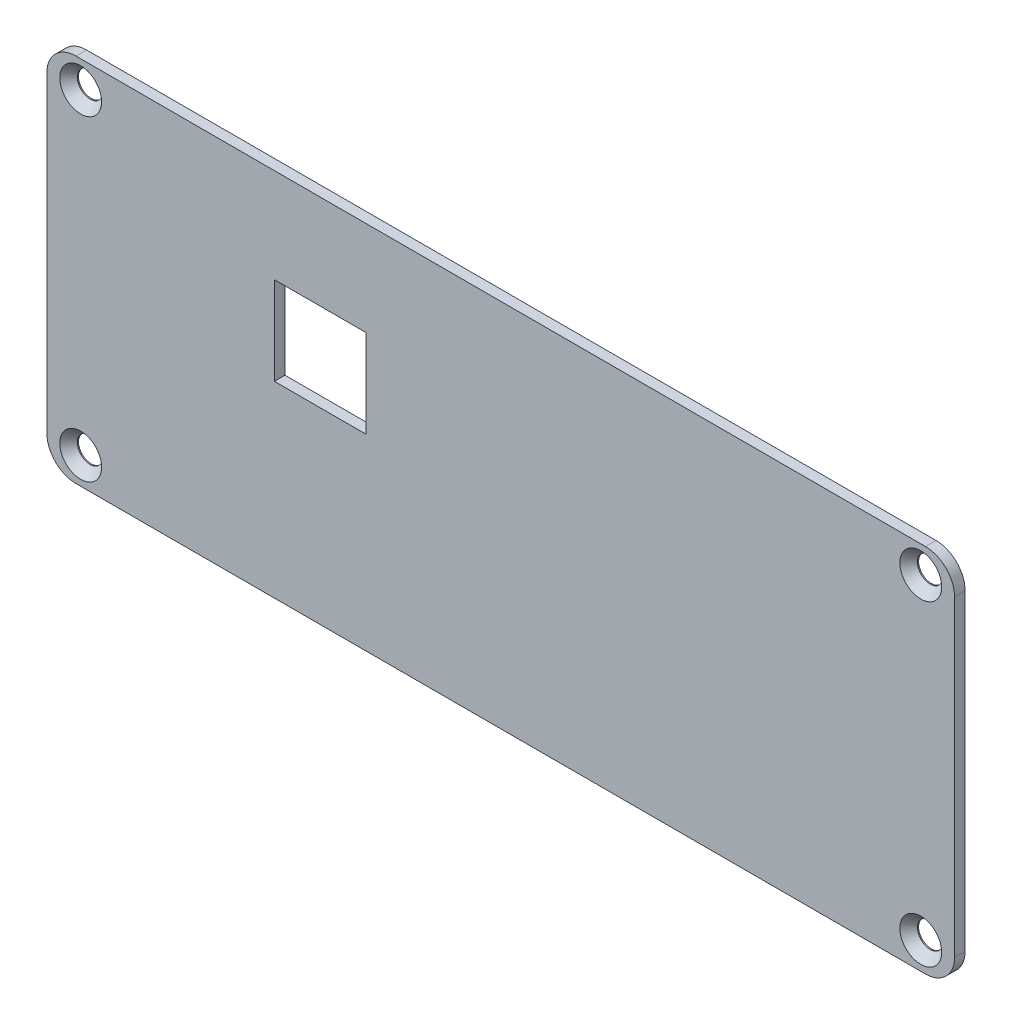
SolidWorks part; units mm, degrees
other "Markup1"
sketch "Sketch3" plane through (0, 0, 0) normal (-0.9973, 0.0561, -0.0476) x (-0.0483, -0.0106, 0.9988)
ref_plane "Front Plane" through (0, 0, 0) normal (0, 0, 1) x (1, 0, 0)
ref_plane "Top Plane" through (0, 0, 0) normal (0, 1, 0) x (1, 0, 0)
ref_plane "Right Plane" through (0, 0, 0) normal (1, 0, 0) x (0, 0, -1)
sketch "Sketch1" plane through (0, 0, 0) normal (0, 0, 1) x (1, 0, 0)
  line L1 (0, 0) -> (124.8, 0)
  line L2 (0, 0) -> (0, -50.9)
  line L3 (0, -50.9) -> (124.8, -50.9)
  line L4 (124.8, 0) -> (124.8, -50.9)
  line L17 (31.285, -12.985) -> (43.885, -12.985)
  line L18 (31.285, -12.985) -> (31.285, -25.085)
  line L19 (31.285, -25.085) -> (43.885, -25.085)
  line L20 (43.885, -12.985) -> (43.885, -25.085)
  point P5 (37.585, -19.035)
  point P6 (0, 0)
  point P7 (37.585, -12.985)
  point P8 (43.885, -19.035)
  dimension "D1" = 124.8
  dimension "D2" = 50.9
  dimension "D3" = 37.585
  dimension "D4" = 19.035
  dimension "D5" = 37.585
  dimension "D6" = 19.035
  dimension "D7" = 12.6
  dimension "D8" = 12.1
extrude "Boss-Extrude1" add sketch "Sketch1" along normal blind 1.45
hole_wizard "CSK for M3.5 Flat Head Machine Screw1" positions "3DSketch1" profile "Sketch2" countersink size "M3.5" standard "ANSI Metric" end condition through all
sketch3d "3DSketch1"
  line L3 (0, 0, 1.45) -> (124.8, 0, 1.45) construction
  line L4 (124.8, 0, 1.45) -> (124.8, -50.9, 1.45) construction
  point P0 (4.65, -3.7, 1.45)
  point P2 (120.15, -3.7, 1.45)
  point P4 (120.15, -47.2, 1.45)
  point P6 (4.65, -47.2, 1.45)
  point P18 (0, 0, 0)
  point P19 (0, 0, 0)
  point P20 (0, 0, 0)
  point P21 (0, 0, 0)
  point P22 (0, 0, 0)
  point P23 (0, 0, 0)
  point P24 (0, 0, 0)
  point P25 (0, 0, 0)
  point P26 (0, 0, 0)
  dimension "D1" = 115.5
  dimension "D2" = 43.5
  dimension "D3" = 3.7
  dimension "D4" = 4.65
sketch "Sketch2" plane through (4.65, -3.7, 1.45) normal (1, 0, 0) x (0, -1, 0)
  line L0 (0, 0) -> (0, 1.45)
  line L1 (0, 1.45) -> (1.75, 1.45)
  line L2 (1.75, 1.45) -> (1.75, 1.2942)
  line L3 (1.75, 1.2942) -> (2.875, 0)
  line L5 (2.875, 0) -> (0, 0)
  line L6 (-1.75, 1.2942) -> (-2.875, 0) construction
  line L11 (0, -6.35) -> (0, 107.95) construction
  dimension "Thru Hole Dia." = 3.5
  dimension "Thru Hole Depth" = 1.45
  dimension "Near C'Sink Dia." = 5.75
  dimension "Near C'Sink Angle" = 82
fillet "Fillet2" radius 4 4 edges at (0, 0, 0.725) (124.8, 0, 0.725) (124.8, -50.9, 0.725) (0, -50.9, 0.725)
